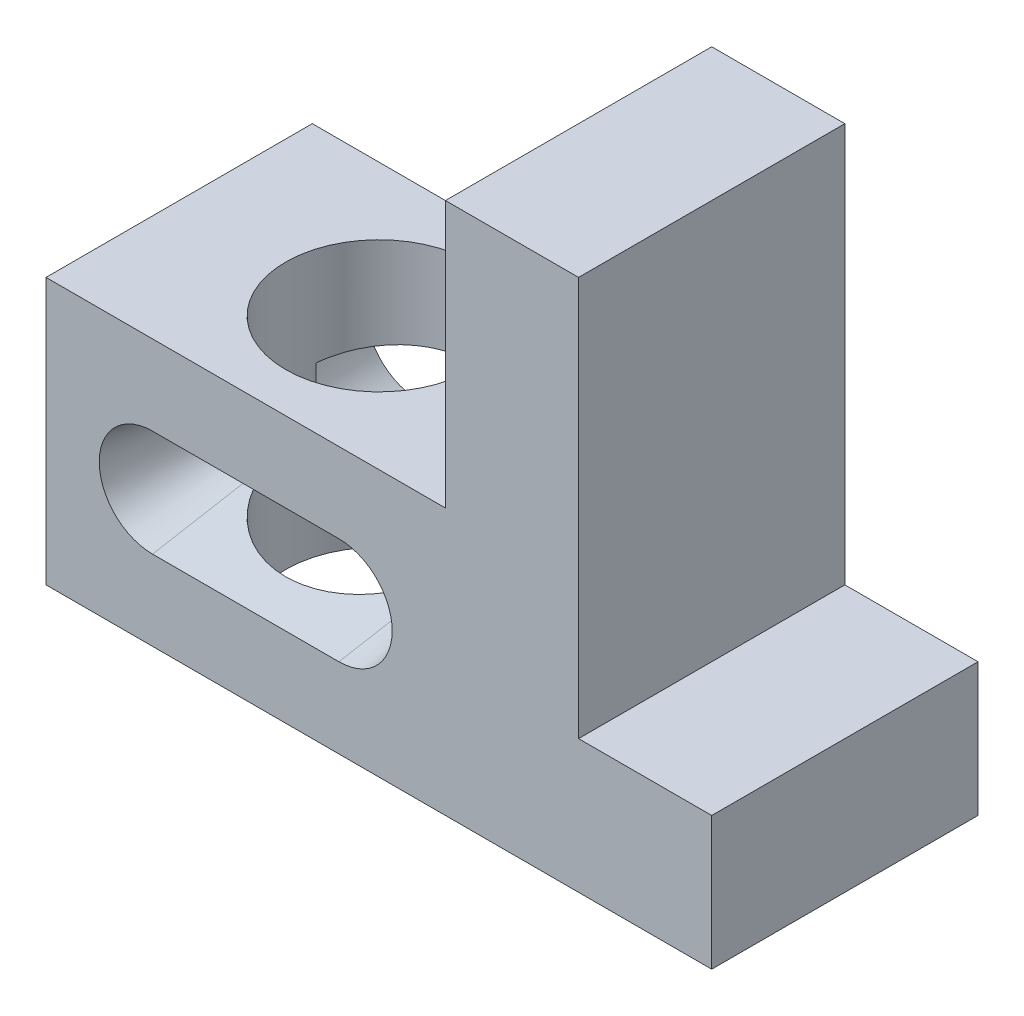
SolidWorks part; units mm, degrees
ref_plane "Front Plane" through (0, 0, 0) normal (0, 0, 1) x (1, 0, 0)
ref_plane "Top Plane" through (0, 0, 0) normal (0, 1, 0) x (1, 0, 0)
ref_plane "Right Plane" through (0, 0, 0) normal (1, 0, 0) x (0, 0, -1)
sketch "Base Sketch" plane through (0, 0, 0) normal (0, 0, 1) x (1, 0, 0)
  line L0 (0, 0) -> (0, 50)
  line L1 (0, 50) -> (75, 50)
  line L2 (75, 50) -> (75, 100)
  line L3 (75, 100) -> (100, 100)
  line L4 (100, 100) -> (100, 25)
  line L5 (100, 25) -> (125, 25)
  line L6 (125, 25) -> (125, 0)
  line L7 (125, 0) -> (0, 0)
  dimension "D1" = 50
  dimension "D2" = 75
  dimension "D3" = 100
  dimension "D4" = 25
  dimension "D5" = 25
extrude "Base Extrusion" add sketch "Base Sketch" along normal blind 50
sketch "Front Cut Sketch" plane through (0, 0, 50) normal (0, 0, 1) x (1, 0, 0)
  line L0 (20, 25) -> (55, 25) construction
  line L1 (20, 35) -> (55, 35)
  line L2 (20, 15) -> (55, 15)
  arc A0 (20, 35) -> (20, 15) centre (20, 25) ccw
  arc A1 (55, 15) -> (55, 35) centre (55, 25) ccw
  point P2 (37.5, 25)
  dimension "D3" = 10
  dimension "D1" = 25
  dimension "D2" = 37.5
  dimension "D4" = 35
extrude "Front Cut" cut sketch "Front Cut Sketch" against normal blind 20 draft 10
sketch "Back Cut Sketch" plane through (0, 0, 0) normal (0, 0, -1) x (-1, 0, 0)
  line L0 (-20, 15) -> (-55, 15) construction
  line L1 (-55, 35) -> (-20, 35) construction
  line L2 (-20, 15) -> (-55, 15)
  line L3 (-55, 35) -> (-20, 35)
  arc A0 (-55, 35) -> (-55, 15) centre (-55, 25) ccw construction
  arc A1 (-20, 15) -> (-20, 35) centre (-20, 25) ccw construction
  arc A2 (-55, 35) -> (-55, 15) centre (-55, 25) ccw
  arc A3 (-20, 15) -> (-20, 35) centre (-20, 25) ccw
extrude "Back Cut" cut sketch "Back Cut Sketch" against normal blind 20 draft 10
sketch "Top Cut Sketch" plane through (0, 50, 0) normal (0, 1, 0) x (1, 0, 0)
  line L0 (75, 0) -> (0, 0) construction
  line L1 (0, -50) -> (0, 0) construction
  circle A0 centre (37.5, -25) radius 17.5
  dimension "D1" = 35
  dimension "D2" = 25
  dimension "D3" = 37.5
extrude "Top Cut" cut sketch "Top Cut Sketch" against normal blind 50
